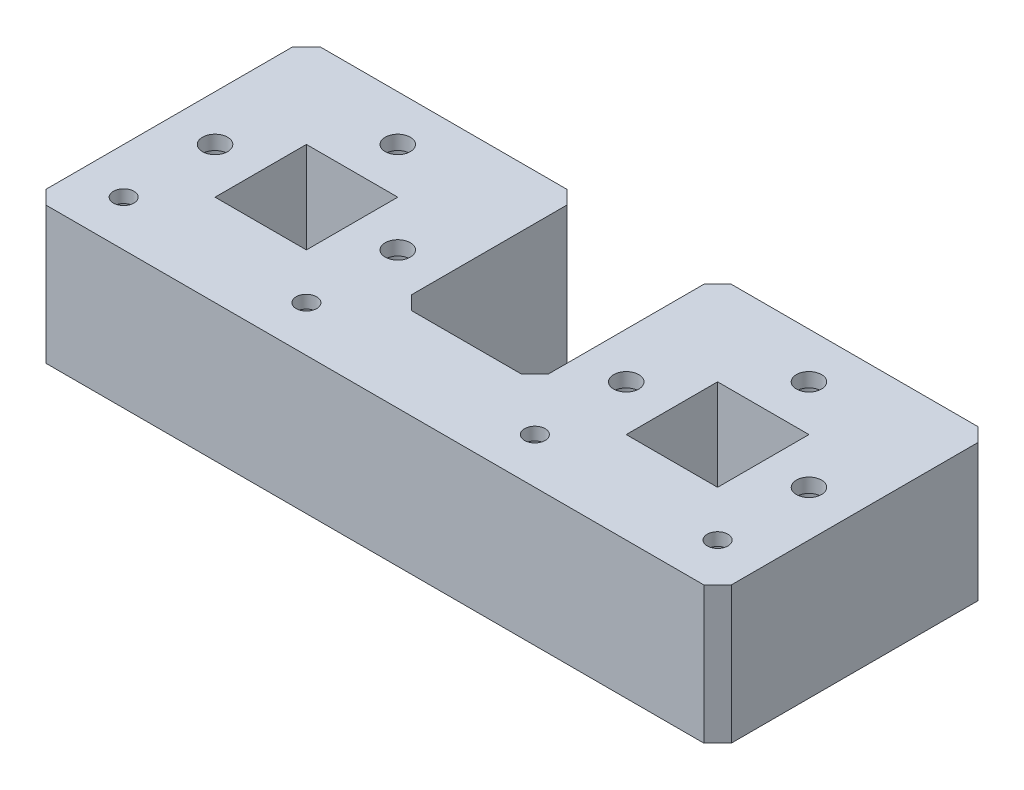
SolidWorks part; units mm, degrees
ref_plane "Ebene vorne" through (0, 0, 0) normal (0, 0, 1) x (1, 0, 0)
ref_plane "Ebene oben" through (0, 0, 0) normal (0, 1, 0) x (1, 0, 0)
ref_plane "Ebene rechts" through (0, 0, 0) normal (1, 0, 0) x (0, 0, -1)
sketch "Skizze1" plane through (0, 0, 0) normal (0, 1, 0) x (1, 0, 0)
  line L0 (0, -10) -> (0, -30)
  line L1 (-75, 30) -> (-15, 30)
  line L2 (-75, 30) -> (-75, -30)
  line L3 (-75, -30) -> (0, -30)
  line L5 (-55, 10) -> (-35, 10)
  line L6 (-55, 10) -> (-55, -10)
  line L7 (-55, -10) -> (-35, -10)
  line L8 (-35, 10) -> (-35, -10)
  line L10 (-15, 30) -> (-15, -10)
  line L11 (-15, -10) -> (0, -10)
  dimension "D1" = 60
  dimension "D3" = 20
  dimension "D4" = 20
  dimension "D5" = 20
  dimension "D6" = 20
  dimension "D7" = 20
extrude "Aufsatz-Linear austragen1" add sketch "Skizze1" along normal blind 30
hole_wizard "Stirnsenkung für M5 Zylinderschraube mit Innensechskant1" positions "Skizze4" profile "Skizze5" counterbore size "M5" standard "DIN" end condition through all
sketch "Skizze4" plane through (0, 0, 0) normal (0, -1, 0) x (-1, 0, 0)
  line L0 (35, -10) -> (35, 10) construction
  line L1 (15, 30) -> (75, 30) construction
  line L2 (35, 10) -> (55, 10) construction
  line L3 (55, 10) -> (55, -10) construction
  point P0 (45, 20)
  point P2 (25, 0)
  point P4 (65, 0)
  point P11 (45, 30)
  dimension "D1" = 10
  dimension "D2" = 10
  dimension "D3" = 10
  dimension "D4" = 10
  dimension "D5" = 10
  dimension "D6" = 10
sketch "Skizze5" plane through (-45, 0, -20) normal (1, 0, 0) x (0, 0, -1)
  line L0 (0, 0) -> (0, 30)
  line L1 (0, 30) -> (2.75, 30)
  line L3 (2.75, 30) -> (2.75, 26.9)
  line L4 (2.75, 26.9) -> (5, 26.9)
  line L5 (5, 26.9) -> (5, 0)
  line L7 (5, 0) -> (0, 0)
  line L11 (0, -6.35) -> (0, 107.95) construction
  dimension "Bohrerdurchmesser" = 5.5
  dimension "Bohrungstiefe" = 30
  dimension "Senkdurchmesser2" = 10
  dimension "Senktiefe2" = 26.9
hole_wizard "Stirnsenkung für M4 Zylinderschraube mit Innensechskant1" positions "Skizze6" profile "Skizze7" counterbore size "M4" standard "DIN" end condition through all
sketch "Skizze6" plane through (0, 0, 0) normal (0, -1, 0) x (-1, 0, 0)
  line L0 (75, -30) -> (0, -30) construction
  line L1 (35, -10) -> (35, 10) construction
  line L2 (55, 10) -> (55, -10) construction
  point P0 (25, -20)
  point P2 (65, -20)
  point P7 (0, 0)
  dimension "D1" = 10
  dimension "D2" = 10
  dimension "D3" = 10
  dimension "D4" = 10
sketch "Skizze7" plane through (-25, 0, 20) normal (1, 0, 0) x (0, 0, -1)
  line L0 (0, 0) -> (0, 30)
  line L1 (0, 30) -> (2.25, 30)
  line L3 (2.25, 30) -> (2.25, 27.2)
  line L4 (2.25, 27.2) -> (4, 27.2)
  line L5 (4, 27.2) -> (4, 0)
  line L7 (4, 0) -> (0, 0)
  line L11 (0, -6.35) -> (0, 107.95) construction
  dimension "Bohrerdurchmesser" = 4.5
  dimension "Bohrungstiefe" = 30
  dimension "Senkdurchmesser2" = 8
  dimension "Senktiefe2" = 27.2
chamfer "Fase1" distance 3 angle 45 4 edges at (-15, 15, 10) (-15, 15, -30) (-75, 15, -30) (-75, 15, 30)
mirror "Spiegeln2" about plane through (0, 0, 0) normal (1, 0, 0) of "Stirnsenkung für M5 Zylinderschraube mit Innensechskant1", "Stirnsenkung für M4 Zylinderschraube mit Innensechskant1", "Fase1", "Aufsatz-Linear austragen1"
